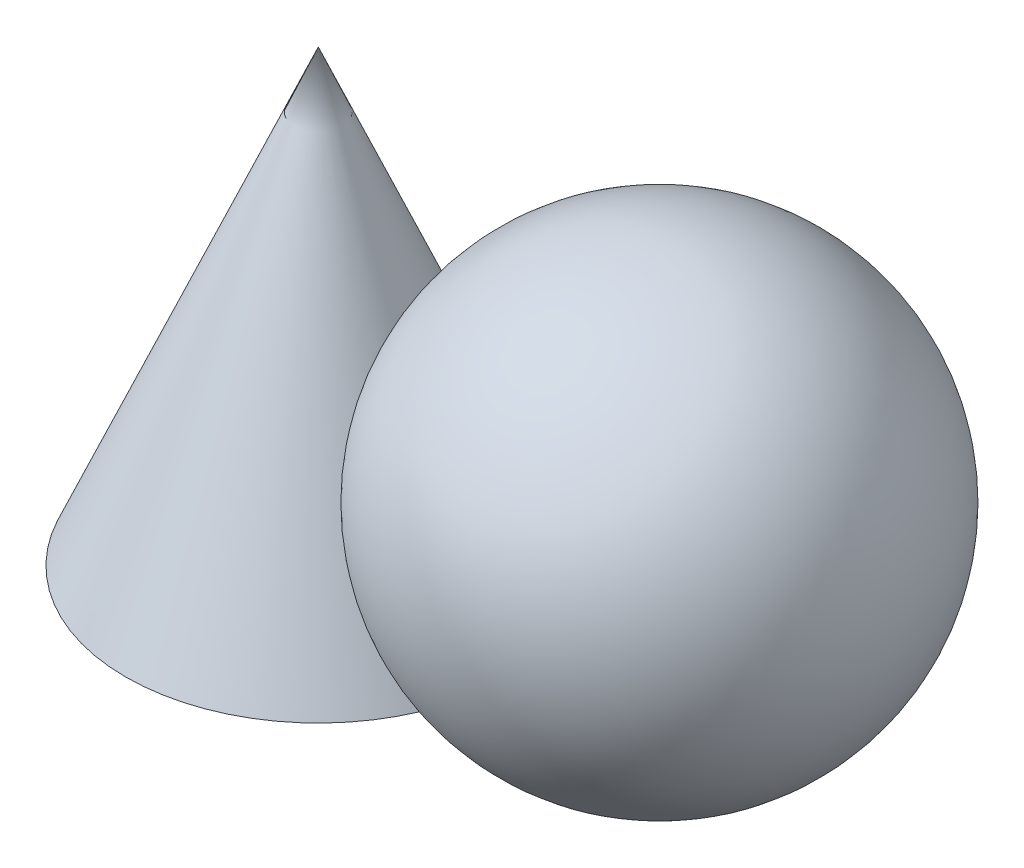
SolidWorks part; units mm, degrees
ref_plane "Front Plane" through (0, 0, 0) normal (0, 0, 1) x (1, 0, 0)
ref_plane "HP" through (0, 0, 0) normal (0, 1, 0) x (1, 0, 0)
ref_plane "Right Plane" through (0, 0, 0) normal (1, 0, 0) x (0, 0, -1)
sketch "Sketch1" plane through (0, 0, 0) normal (0, 1, 0) x (1, 0, 0)
  circle A0 centre (0, 0) radius 30
  dimension "D1" = 60
ref_plane "Plane1" through (0, 70, 0) normal (0, 1, 0) x (1, 0, 0)
sketch "Sketch2" plane through (0, 70, 0) normal (0, 1, 0) x (1, 0, 0)
  point P0 (0, 0)
loft "Loft1" add profiles "Sketch2", "Sketch1"
sketch "Point P" plane through (0, 0, 0) normal (0, 0, 1) x (1, 0, 0)
  line L0 (30, 0) -> (0, 70) construction
  point P0 (21, 21)
  dimension "D1" = 21
sketch "Sketch5" plane through (0, 0, 0) normal (0, 0, 1) x (1, 0, 0)
  line L0 (0, 0) -> (84.5491, 0) construction
  line L1 (53.1373, 70.1814) -> (53.1373, 0) construction
  line L2 (53.1373, 70.1814) -> (53.1373, 0)
  arc A0 (53.1373, 70.1814) -> (53.1373, 0) centre (53.1373, 35.0907) ccw
revolve "Revolve2" add sketch "Sketch5" angle 360 about L2
